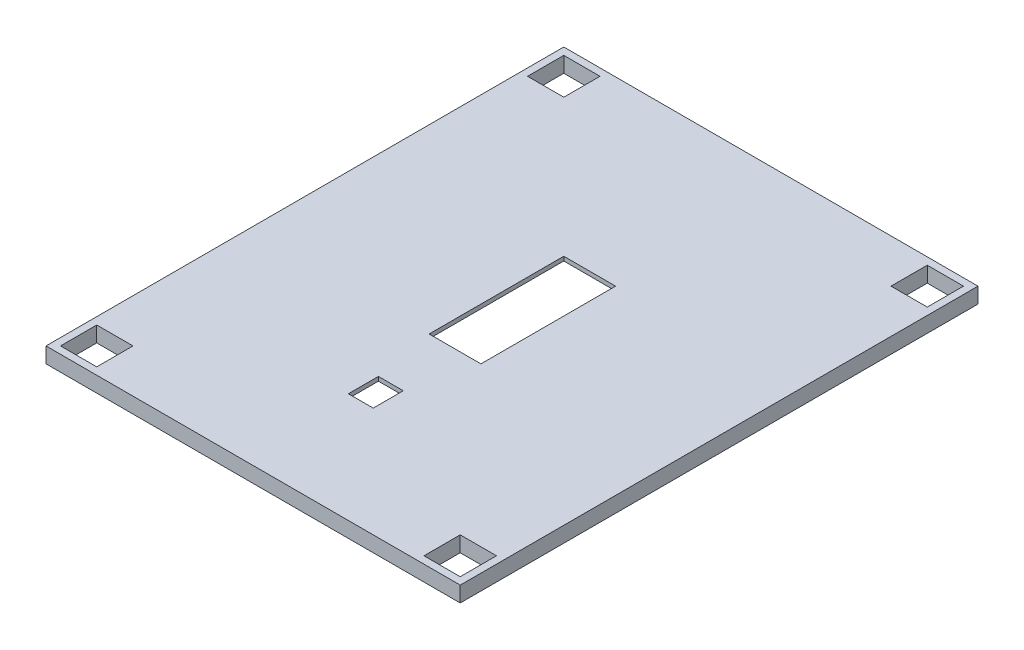
SolidWorks part; units mm, degrees
ref_plane "Front Plane" through (0, 0, 0) normal (0, 0, 1) x (1, 0, 0)
ref_plane "Top Plane" through (0, 0, 0) normal (0, 1, 0) x (1, 0, 0)
ref_plane "Right Plane" through (0, 0, 0) normal (1, 0, 0) x (0, 0, -1)
sketch "Sketch1" plane through (0, 0, 0) normal (0, 1, 0) x (1, 0, 0)
  line L1 (0, 0) -> (80, 0)
  line L2 (0, 0) -> (0, 100)
  line L3 (0, 100) -> (80, 100)
  line L4 (80, 0) -> (80, 100)
  dimension "D1" = 100
  dimension "D2" = 80
extrude "Boss-Extrude1" add sketch "Sketch1" along normal blind 3
sketch "Sketch2" plane through (0, 0, 0) normal (0, -1, 0) x (1, 0, 0)
  line L0 (0, 0) -> (80, 0) construction
  line L1 (1.6, -1.6) -> (78.4, -1.6)
  line L2 (1.6, -1.6) -> (1.6, -98.4)
  line L3 (1.6, -98.4) -> (78.4, -98.4)
  line L4 (78.4, -1.6) -> (78.4, -98.4)
  line L5 (0, -100) -> (0, 0) construction
  line L6 (80, -100) -> (0, -100) construction
  line L7 (80, 0) -> (80, -100) construction
  dimension "D1" = 1.6
  dimension "D2" = 1.6
  dimension "D3" = 1.6
  dimension "D4" = 1.6
extrude "Cut-Extrude1" cut sketch "Sketch2" against normal offset from surface (2.2 mm away) 0.8 up to face at (40, 3, -50)
sketch "Sketch5" plane through (0, 3, 0) normal (0, 1, 0) x (1, 0, 0)
  line L1 (35, 65) -> (45, 65)
  line L2 (35, 65) -> (35, 39)
  line L3 (35, 39) -> (45, 39)
  line L4 (45, 65) -> (45, 39)
  line L5 (80, 100) -> (0, 100) construction
  line L6 (80, 0) -> (80, 100) construction
  line L7 (37.2, 27) -> (42, 27)
  line L8 (37.2, 27) -> (37.2, 21.2)
  line L9 (37.2, 21.2) -> (42, 21.2)
  line L10 (42, 27) -> (42, 21.2)
  dimension "D1" = 10
  dimension "D2" = 26
  dimension "D3" = 35
  dimension "D4" = 35
  dimension "D5" = 12
  dimension "D6" = 4.8
  dimension "D7" = 5.8
  dimension "D8" = 3
extrude "Cut-Extrude2" cut sketch "Sketch5" against normal up to next
sketch "Sketch7" plane through (0, 0, -100) normal (0, 0, -1) x (-1, 0, 0)
  line L0 (-80, 0) -> (0, 0) construction
  line L1 (-42.75, 2.2) -> (-37.25, 2.2)
  line L2 (-42.75, 2.2) -> (-42.75, 0)
  line L3 (-42.75, 0) -> (-37.25, 0)
  line L4 (-37.25, 2.2) -> (-37.25, 0)
  line L5 (-80, 3) -> (0, 3) construction
  line L6 (-80, 3) -> (-80, 0) construction
  dimension "D1" = 0.8
  dimension "D2" = 5.5
  dimension "D3" = 37.25
extrude "Cut-Extrude4" cut sketch "Sketch7" against normal blind 3
sketch "Sketch9" plane through (0, 2.2, 0) normal (0, -1, 0) x (1, 0, 0)
  line L0 (1.6, -1.6) -> (78.4, -1.6) construction
  line L1 (1.6, -1.6) -> (9.8, -1.6)
  line L2 (1.6, -1.6) -> (1.6, -9.8)
  line L3 (1.6, -9.8) -> (9.8, -9.8)
  line L4 (9.8, -1.6) -> (9.8, -9.8)
  line L5 (70.2, -1.6) -> (78.4, -1.6)
  line L6 (70.2, -1.6) -> (70.2, -9.8)
  line L7 (70.2, -9.8) -> (78.4, -9.8)
  line L8 (78.4, -1.6) -> (78.4, -9.8)
  line L9 (1.6, -1.6) -> (1.6, -98.4) construction
  line L10 (1.6, -90.2) -> (9.8, -90.2)
  line L11 (1.6, -90.2) -> (1.6, -98.4)
  line L12 (1.6, -98.4) -> (9.8, -98.4)
  line L13 (9.8, -90.2) -> (9.8, -98.4)
  line L14 (37.25, -98.4) -> (1.6, -98.4) construction
  line L15 (78.4, -98.4) -> (78.4, -1.6) construction
  line L16 (70.2, -90.2) -> (78.4, -90.2)
  line L17 (70.2, -90.2) -> (70.2, -98.4)
  line L18 (70.2, -98.4) -> (78.4, -98.4)
  line L19 (78.4, -90.2) -> (78.4, -98.4)
  dimension "D1" = 8.2
  dimension "D2" = 8.2
  dimension "D3" = 8.2
  dimension "D4" = 8.2
  dimension "D5" = 8.2
  dimension "D6" = 8.2
  dimension "D7" = 8.2
  dimension "D8" = 8.2
extrude "Boss-Extrude2" add sketch "Sketch9" along normal up to surface (2.2 mm away) up to face at (40, 0, -66.4)
sketch "Sketch10" plane through (0, 0, 0) normal (0, -1, 0) x (1, 0, 0)
  line L0 (0, 0) -> (80, 0) construction
  line L1 (1.4, -1.4) -> (8.4, -1.4)
  line L2 (1.4, -1.4) -> (1.4, -8.4)
  line L3 (1.4, -8.4) -> (8.4, -8.4)
  line L4 (8.4, -1.4) -> (8.4, -8.4)
  line L5 (1.6, -9.8) -> (9.8, -9.8) construction
  line L6 (0, -100) -> (0, 0) construction
  line L7 (9.8, -9.8) -> (9.8, -1.6) construction
  line L8 (9.8, -90.2) -> (1.6, -90.2) construction
  line L9 (1.4, -91.6) -> (8.4, -91.6)
  line L10 (1.4, -91.6) -> (1.4, -98.6)
  line L11 (1.4, -98.6) -> (8.4, -98.6)
  line L12 (8.4, -91.6) -> (8.4, -98.6)
  line L13 (9.8, -98.4) -> (9.8, -90.2) construction
  line L14 (37.25, -100) -> (0, -100) construction
  line L15 (80, 0) -> (80, -100) construction
  line L16 (71.6, -91.6) -> (78.6, -91.6)
  line L17 (71.6, -91.6) -> (71.6, -98.6)
  line L18 (71.6, -98.6) -> (78.6, -98.6)
  line L19 (78.6, -91.6) -> (78.6, -98.6)
  line L20 (70.2, -90.2) -> (70.2, -98.4) construction
  line L21 (80, -100) -> (42.75, -100) construction
  line L22 (78.4, -90.2) -> (70.2, -90.2) construction
  line L23 (70.2, -9.8) -> (78.4, -9.8) construction
  line L24 (71.6, -1.4) -> (78.6, -1.4)
  line L25 (71.6, -1.4) -> (71.6, -8.4)
  line L26 (71.6, -8.4) -> (78.6, -8.4)
  line L27 (78.6, -1.4) -> (78.6, -8.4)
  line L28 (70.2, -1.6) -> (70.2, -9.8) construction
  dimension "D1" = 1.4
  dimension "D2" = 1.4
  dimension "D3" = 1.4
  dimension "D4" = 1.4
  dimension "D5" = 1.4
  dimension "D6" = 1.4
  dimension "D7" = 1.4
  dimension "D8" = 1.4
  dimension "D9" = 1.4
  dimension "D10" = 1.4
  dimension "D11" = 1.4
  dimension "D12" = 1.4
  dimension "D13" = 1.4
  dimension "D14" = 1.4
  dimension "D15" = 1.4
extrude "Cut-Extrude5" cut sketch "Sketch10" against normal through all
